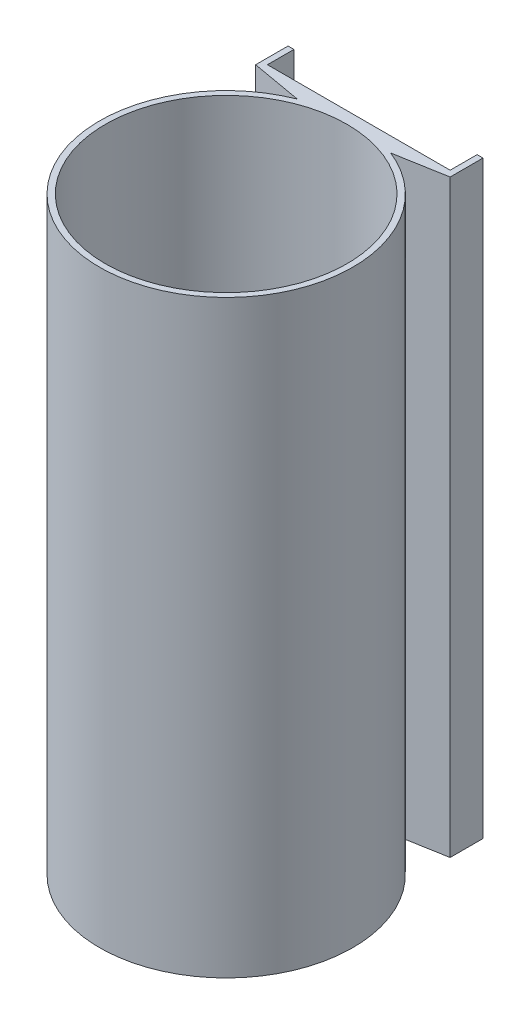
SolidWorks part; units mm, degrees
ref_plane "Front Plane" through (0, 0, 0) normal (0, 0, 1) x (1, 0, 0)
ref_plane "Top Plane" through (0, 0, 0) normal (0, 1, 0) x (1, 0, 0)
ref_plane "Right Plane" through (0, 0, 0) normal (1, 0, 0) x (0, 0, -1)
sketch "Sketch3" plane through (0, 0, 0) normal (0, 1, 0) x (1, 0, 0)
  line L2 (33, 43) -> (15.8434, 39.9748)
  line L3 (-33, 43) -> (-15.8434, 39.9748)
  line L4 (-33, 43) -> (-33, 54)
  line L5 (33, 43) -> (33, 54.1591)
  line L6 (-33, 54) -> (-31, 54)
  line L7 (-31, 54) -> (-31, 45)
  line L8 (-31, 45) -> (31, 45)
  line L9 (31, 45) -> (31, 54.1591)
  line L10 (31, 54.1591) -> (33, 54.1591)
  circle A0 centre (0, 0) radius 43
  circle A1 centre (0, 0) radius 41
  point P7 (0, 0)
  dimension "D1" = 82
  dimension "D2" = 86
  dimension "D3" = 2
  dimension "D5" = 2
extrude "Boss-Extrude1" add sketch "Sketch3" along normal blind 200 contours A0 L2 L5 L10 L9 L8 L7 L6 L4 L3 | A0 A1
